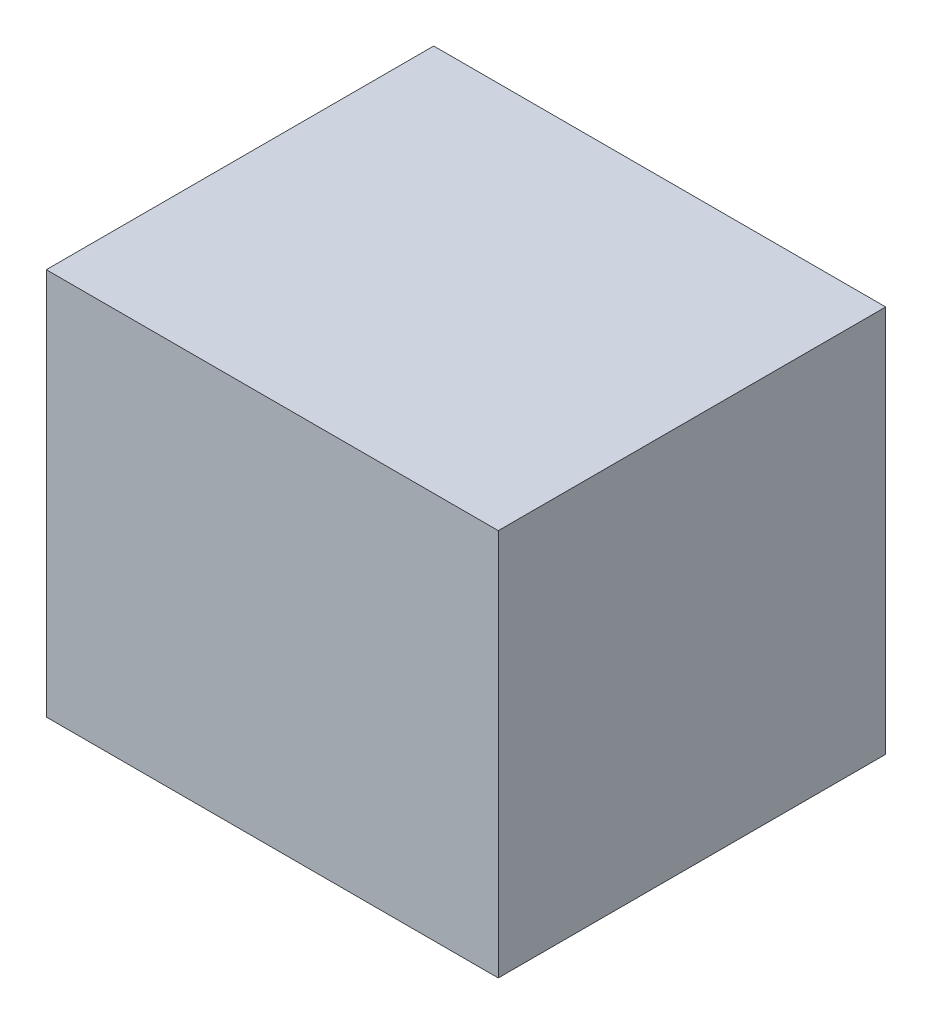
SolidWorks part; units mm, degrees
ref_plane "Front Plane" through (0, 0, 0) normal (0, 0, 1) x (1, 0, 0)
ref_plane "Top Plane" through (0, 0, 0) normal (0, 1, 0) x (1, 0, 0)
ref_plane "Right Plane" through (0, 0, 0) normal (1, 0, 0) x (0, 0, -1)
sketch "Sketch1" plane through (0, 0, 0) normal (1, 0, 0) x (0, 0, -1)
  line L1 (38.1, 38.1) -> (-38.1, 38.1)
  line L2 (38.1, 38.1) -> (38.1, -38.1)
  line L3 (38.1, -38.1) -> (-38.1, -38.1)
  line L4 (-38.1, 38.1) -> (-38.1, -38.1)
  line L5 (38.1, 38.1) -> (-38.1, -38.1) construction
  line L6 (38.1, -38.1) -> (-38.1, 38.1) construction
  point P0 (0, 0)
  dimension "D1" = 76.2
  dimension "D2" = 76.2
extrude "Boss-Extrude1" add sketch "Sketch1" along normal blind 88.9
